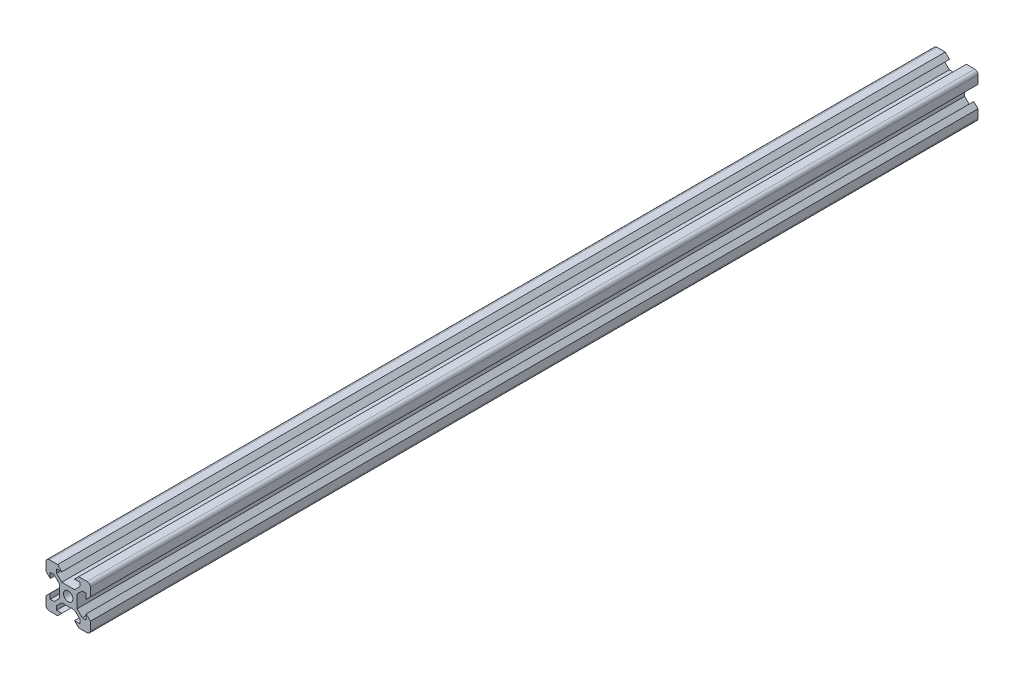
SolidWorks part; units mm, degrees
material "6061 Alloy"
ref_plane "Front Plane" through (0, 0, 0) normal (0, 0, 1) x (1, 0, 0)
ref_plane "Top Plane" through (0, 0, 0) normal (0, 1, 0) x (1, 0, 0)
ref_plane "Right Plane" through (0, 0, 0) normal (1, 0, 0) x (0, 0, -1)
sketch "Sketch1" plane through (0, 0, 0) normal (0, 0, 1) x (1, 0, 0)
  line L0 (15.6876, 55.3211) -> (115.0437, 55.3211) construction
  line L1 (8.1, 5.225) -> (8.1, 2.85)
  line L2 (-8.5, 10) -> (-4.75, 10)
  line L3 (-10, 8.5) -> (-10, 4.75)
  line L4 (-8.5, -10) -> (-4.75, -10)
  line L5 (10, 8.5) -> (10, 4.75)
  line L6 (6.325, 5.225) -> (4, 2.9)
  line L7 (-8.1, -2.85) -> (-8.1, -5.225)
  line L8 (-2.9, 4) -> (2.9, 4)
  line L9 (-4, 2.9) -> (-4, -2.9)
  line L10 (-2.9, -4) -> (2.9, -4)
  line L11 (4, 2.9) -> (4, -2.9)
  line L12 (2.85, -8.1) -> (5.225, -8.1)
  line L13 (-5.225, -8.1) -> (-2.85, -8.1)
  line L14 (5.225, 6.325) -> (2.9, 4)
  line L17 (-10, 4.75) -> (-8.1, 2.85)
  line L20 (4.75, -10) -> (8.5, -10)
  line L22 (-10, -4.75) -> (-10, -8.5)
  line L23 (10, -4.75) -> (10, -8.5)
  line L24 (-10, -4.75) -> (-8.1, -2.85)
  line L25 (-4.75, -10) -> (-2.85, -8.1)
  line L26 (4.75, -10) -> (2.85, -8.1)
  line L27 (10, -4.75) -> (8.1, -2.85)
  line L28 (10, 4.75) -> (8.1, 2.85)
  line L29 (-4.75, 10) -> (-2.85, 8.1)
  line L30 (4.75, 10) -> (2.85, 8.1)
  line L31 (8.1, -2.85) -> (8.1, -5.225)
  line L32 (6.325, -5.225) -> (8.1, -5.225)
  line L33 (5.225, -6.325) -> (5.225, -8.1)
  line L34 (4.75, 10) -> (8.5, 10)
  line L35 (2.85, 8.1) -> (5.225, 8.1)
  line L36 (10, -10) -> (10.975, -10.975) construction
  line L37 (-5.225, 8.1) -> (-2.85, 8.1)
  line L38 (-8.1, -5.225) -> (-6.325, -5.225)
  line L39 (-5.225, 6.325) -> (-2.9, 4)
  line L40 (-8.1, 5.225) -> (-8.1, 2.85)
  line L41 (-5.225, -6.325) -> (-5.225, -8.1)
  line L42 (-6.325, 5.225) -> (-4, 2.9)
  line L46 (-8.1, 5.225) -> (-6.325, 5.225)
  line L47 (-5.225, 8.1) -> (-5.225, 6.325)
  line L52 (8.1, 5.225) -> (6.325, 5.225)
  line L53 (5.225, 8.1) -> (5.225, 6.325)
  line L63 (4, -2.9) -> (6.325, -5.225)
  line L66 (2.9, -4) -> (5.225, -6.325)
  line L67 (-2.9, -4) -> (-5.225, -6.325)
  line L70 (-4, -2.9) -> (-6.325, -5.225)
  arc A0 (-8.5, -10) -> (-10, -8.5) centre (-8.5, -8.5) cw
  arc A1 (8.5, -10) -> (10, -8.5) centre (8.5, -8.5) ccw
  arc A2 (10, 8.5) -> (8.5, 10) centre (8.5, 8.5) ccw
  arc A3 (-8.5, 10) -> (-10, 8.5) centre (-8.5, 8.5) ccw
  circle A4 centre (0, 0) radius 2.125
  point P2 (0, 0)
  point P8 (0, 0)
  point P14 (-10, -10)
  point P20 (0, 0)
  point P49 (10, 10)
  point P52 (-10, 10)
  dimension "D3" = 1.5
  dimension "D4" = 4.25
  dimension "D1" = 20
  dimension "D2" = 20
  dimension "D13" = 5.25
  dimension "D14" = 5.25
  dimension "D15" = 90
  dimension "D16" = 5.25
  dimension "D17" = 5.25
  dimension "D18" = 5.25
  dimension "D19" = 5.25
  dimension "D20" = 5.25
  dimension "D21" = 5.25
  dimension "D22" = 90
  dimension "D23" = 90
  dimension "D24" = 90
  dimension "D25" = 2.85
  dimension "D26" = 2.85
  dimension "D27" = 2.85
  dimension "D28" = 2.85
extrude "Boss-Extrude1" add sketch "Sketch1" along normal blind 400
